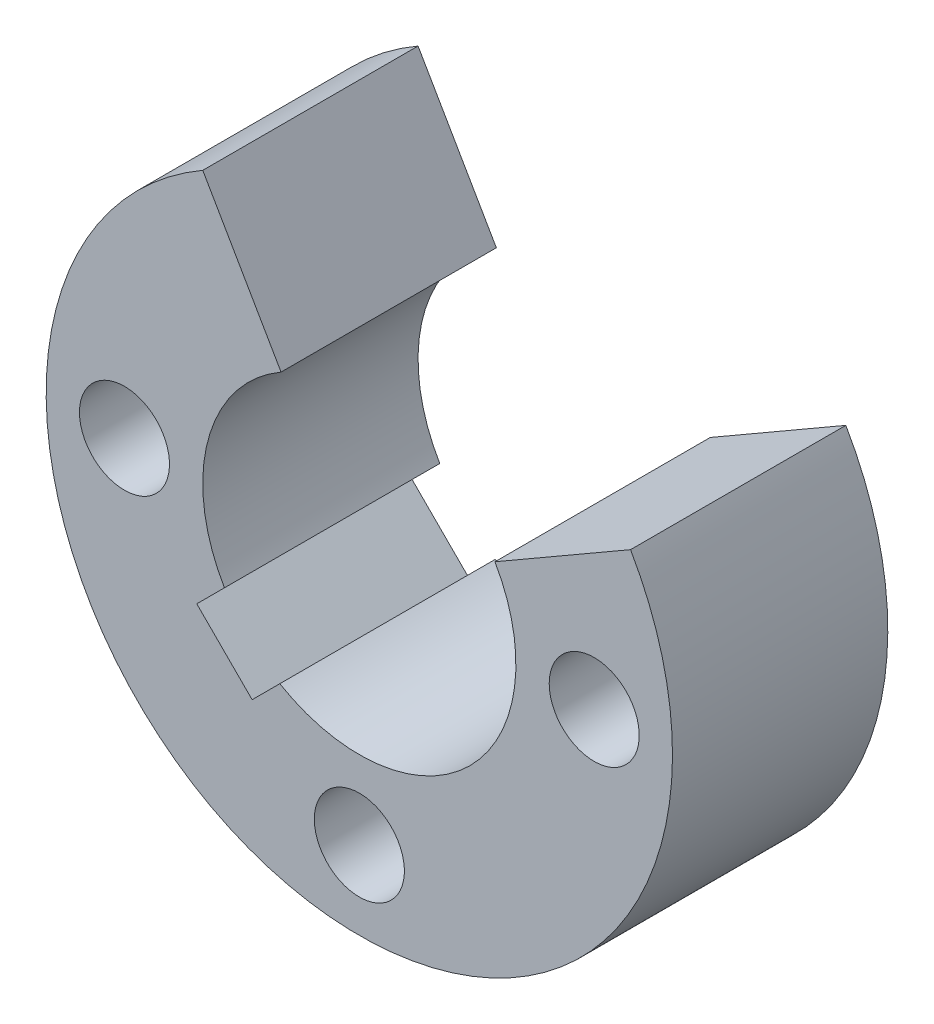
SolidWorks part; units mm, degrees
ref_plane "Front Plane" through (0, 0, 0) normal (0, 0, 1) x (1, 0, 0)
ref_plane "Top Plane" through (0, 0, 0) normal (0, 1, 0) x (1, 0, 0)
ref_plane "Right Plane" through (0, 0, 0) normal (1, 0, 0) x (0, 0, -1)
sketch "Sketch1" plane through (0, 0, 0) normal (0, 0, 1) x (1, 0, 0)
  line L0 (0, 0) -> (0, -42) construction
  line L1 (0, -42) -> (0, -40)
  circle A0 centre (0, 0) radius 8 construction
  circle A1 centre (0, 0) radius 6 construction
  circle A2 centre (0, 6) radius 1.15
  circle A3 centre (-6, 0) radius 1.15
  circle A4 centre (0, -6) radius 1.15
  circle A5 centre (6, 0) radius 1.15
  arc A6 (0, 8) -> (0, -8) centre (0, 0) ccw
  arc A7 (0, 8) -> (0, -42) centre (0, -17) cw
  arc A8 (6.0995, 5.1765) -> (0, -40) centre (0, -17) cw
  arc A9 (0, -8) -> (6.0995, 5.1765) centre (0, 0) ccw
  point P12 (0, 8)
  dimension "D1" = 16
  dimension "D2" = 12
  dimension "D3" = 2.3
  dimension "D4" = 2
  dimension "D5" = 50
extrude "Boss-Extrude1" add sketch "Sketch1" along normal blind 8
sketch "Sketch4" plane through (0, 0, 0) normal (0, 0, -1) x (-1, 0, 0)
  circle A0 centre (0, 0) radius 8
  circle A1 centre (0, 6) radius 1.15 construction
  circle A2 centre (-6, 0) radius 1.15 construction
  circle A3 centre (0, -6) radius 1.15 construction
  circle A4 centre (6, 0) radius 1.15 construction
  circle A5 centre (0, 6) radius 1.15
  circle A6 centre (-6, 0) radius 1.15
  circle A7 centre (0, -6) radius 1.15
  circle A8 centre (6, 0) radius 1.15
extrude "Boss-Extrude2" add sketch "Sketch4" along normal blind 3
sketch "Sketch3" plane through (0, 0, 8) normal (0, 0, 1) x (1, 0, 0)
  line L0 (6, 2) -> (10, 2)
  line L1 (10, 2) -> (10, -2)
  line L2 (10, -2) -> (6, -2)
  line L3 (2, -6) -> (2, -10)
  line L4 (2, -10) -> (-2, -10)
  line L5 (-2, -10) -> (-2, -6)
  line L6 (-6, -2) -> (-10, -2)
  line L7 (-10, -2) -> (-10, 2)
  line L8 (-10, 2) -> (-6, 2)
  line L9 (-2, 6) -> (-2, 10)
  line L10 (-2, 10) -> (2, 10)
  line L11 (2, 10) -> (2, 6)
  circle A0 centre (6, 0) radius 2 construction
  circle A1 centre (0, 6) radius 2 construction
  circle A2 centre (-6, 0) radius 2 construction
  circle A3 centre (0, -6) radius 2 construction
  arc A4 (2, 6) -> (-2, 6) centre (0, 6) cw
  arc A5 (-6, 2) -> (-6, -2) centre (-6, 0) cw
  arc A6 (-2, -6) -> (2, -6) centre (0, -6) cw
  arc A7 (6, -2) -> (6, 2) centre (6, 0) cw
  dimension "D1" = 4
  dimension "D2" = 4
extrude "Cut-Extrude3" cut sketch "Sketch3" against normal offset from surface (5.5 mm away) 5.5 up to face at (-1.15, -6, -3)
sketch "Sketch5" plane through (0, 0, -3) normal (0, 0, -1) x (-1, 0, 0)
  line L0 (-3.4641, 2) -> (-6.9282, 4)
  line L1 (4, 6.9282) -> (2, 3.4641)
  line L7 (2.0315, -3.4457) -> (2.7386, -4.1528)
  line L8 (2.7386, -4.1528) -> (4.1528, -2.7386)
  line L9 (4.1528, -2.7386) -> (3.4457, -2.0315)
  line L10 (0, 0) -> (2.3478, 0) construction
  circle A1 centre (0, 0) radius 8 construction
  arc A2 (-6.9282, 4) -> (4, 6.9282) centre (0, 0) ccw
  arc A3 (-3.4641, 2) -> (2.0315, -3.4457) centre (0, 0) ccw
  arc A4 (3.4457, -2.0315) -> (2, 3.4641) centre (0, 0) ccw
  point P12 (0, 0)
  dimension "D2" = 4
  dimension "D1" = 90
  dimension "D3" = 45
  dimension "D4" = 1
  dimension "D5" = 2
  dimension "D6" = 30
sketch "Sketch6" plane through (0, 0, 8) normal (0, 0, 1) x (1, 0, 0)
  circle A0 centre (0, 0) radius 42
extrude "Cut-Extrude5" cut sketch "Sketch6" against normal up to surface (5.5 mm away) up to face at (4.85, 0, 2.5)
extrude "Cut-Extrude6" cut sketch "Sketch5" against normal through all
